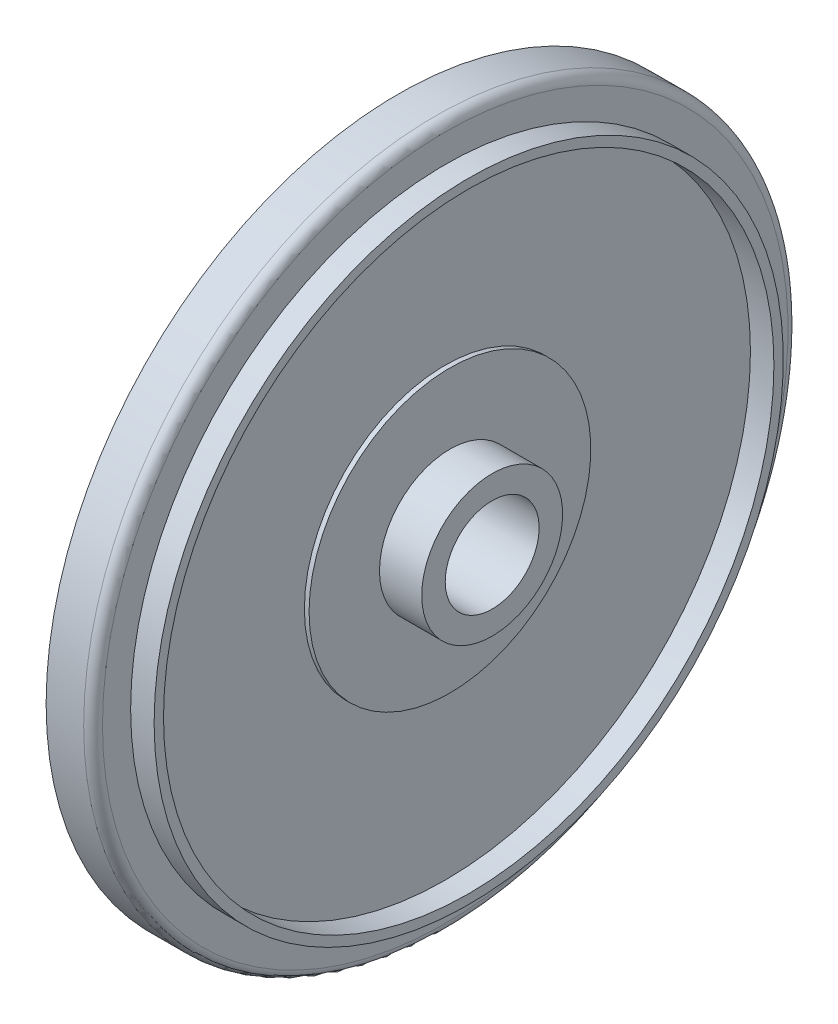
SolidWorks part; units mm, degrees
ref_plane "Front Plane" through (0, 0, 0) normal (0, 0, 1) x (1, 0, 0)
ref_plane "Top Plane" through (0, 0, 0) normal (0, 1, 0) x (1, 0, 0)
ref_plane "Right Plane" through (0, 0, 0) normal (1, 0, 0) x (0, 0, -1)
sketch "Sketch1" plane through (0, 0, 0) normal (0, 0, 1) x (1, 0, 0)
  line L0 (0, 0) -> (6, 0) construction
  line L1 (3, 1) -> (3, 7.5)
  line L2 (3, 7.5) -> (4, 7.5)
  line L3 (4, 7.5) -> (4, 6.7)
  line L4 (4, 6.7) -> (4.5, 6.7)
  line L5 (4.5, 6.7) -> (4.5, 6.5)
  line L6 (4.5, 6.5) -> (4, 6.5)
  line L7 (4, 6.5) -> (4, 3)
  line L8 (4, 3) -> (4.1, 3)
  line L9 (4.1, 3) -> (4.1, 1.5)
  line L10 (4.1, 1.5) -> (5, 1.5)
  line L11 (5, 1.5) -> (5, 1)
  line L12 (5, 1) -> (3, 1)
  point P3 (0, 0)
  point P16 (3, 0)
  dimension "D1" = 15
  dimension "D2" = 2
  dimension "D3" = 1
  dimension "D4" = 0.5
  dimension "D5" = 0.2
  dimension "D6" = 6
  dimension "D7" = 3.5
  dimension "D8" = 0.1
  dimension "D9" = 3
  dimension "D10" = 2
  dimension "D11" = 6
revolve "Revolve1" add sketch "Sketch1" angle 360 about L0
fillet "Fillet1" radius 0.2 1 edges at (4, 0, 7.5)
